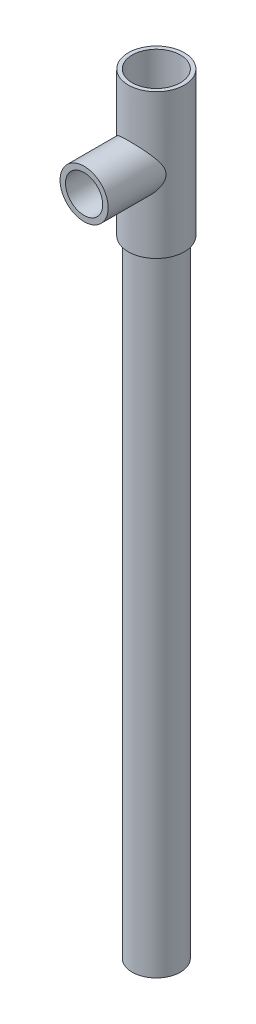
SolidWorks part; units mm, degrees
material "PTFE (general)"
ref_plane "Front Plane" through (0, 0, 0) normal (0, 0, 1) x (1, 0, 0)
ref_plane "Top Plane" through (0, 0, 0) normal (0, 1, 0) x (1, 0, 0)
ref_plane "Right Plane" through (0, 0, 0) normal (1, 0, 0) x (0, 0, -1)
sketch "Sketch1" plane through (0, 0, 0) normal (0, 1, 0) x (1, 0, 0)
  circle A0 centre (0, 0) radius 12.7
  circle A1 centre (0, 0) radius 10.3137
  dimension "D1" = 25.4
extrude "Boss-Extrude1" add sketch "Sketch1" along normal blind 355.6 contours A0 | A1
sketch "Sketch2" plane through (0, 355.6, 0) normal (0, 1, 0) x (1, 0, 0)
  circle A0 centre (0, 0) radius 14.7803
  circle A1 centre (0, 0) radius 12.7138
extrude "Boss-Extrude2" add sketch "Sketch2" along normal blind 50.8 and the other way blind 25.4 separate body
sketch "Sketch3" plane through (0, 0, 0) normal (0, 0, 1) x (1, 0, 0)
  line L0 (0, 406.4) -> (0, 368.3) construction
  line L1 (12.7138, 406.4) -> (-12.7138, 406.4) construction
  circle A0 centre (0, 368.3) radius 12.7
  circle A1 centre (0, 368.3) radius 9.8053
  dimension "D2" = 25.4
  dimension "D1" = 38.1
extrude "Boss-Extrude3" add sketch "Sketch3" along normal blind 38.1
